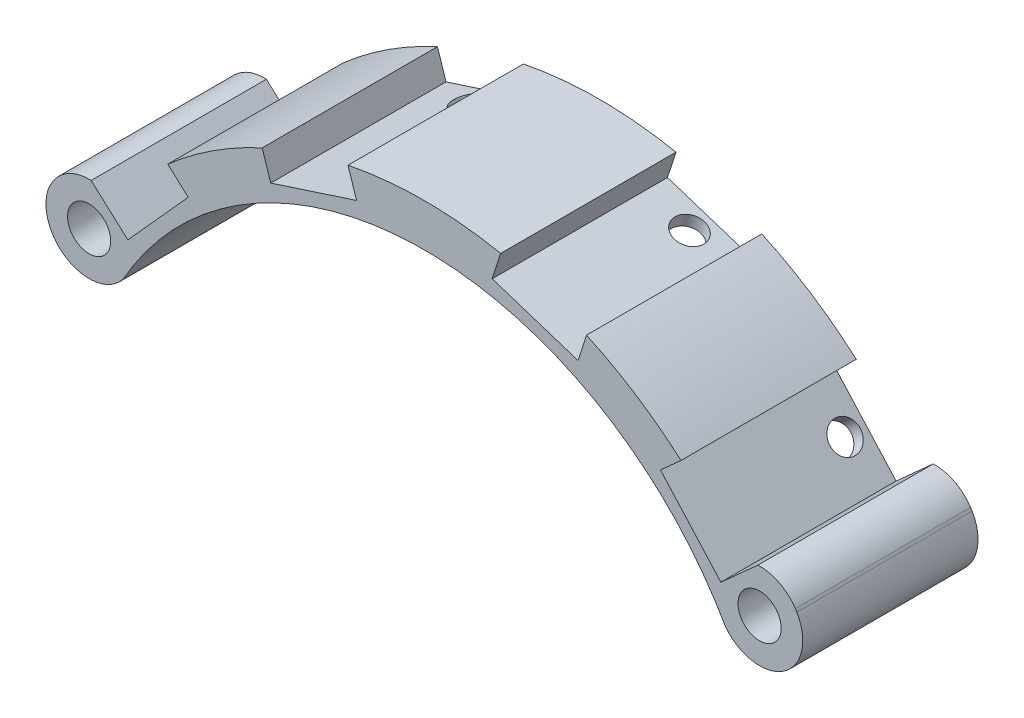
SolidWorks part; units mm, degrees
ref_plane "Plano frontal" through (0, 0, 0) normal (0, 0, 1) x (1, 0, 0)
ref_plane "Plano superior" through (0, 0, 0) normal (0, 1, 0) x (1, 0, 0)
ref_plane "Plano direito" through (0, 0, 0) normal (1, 0, 0) x (0, 0, -1)
sketch "Esboço1" plane through (0, 0, 0) normal (0, 0, 1) x (1, 0, 0)
  line L0 (0, 0) -> (0, 51.8382) construction
  line L1 (-61.8649, 0) -> (70.1374, 0) construction
  line L2 (0, 0) -> (48.4294, 43.606) construction
  line L3 (0, 0) -> (18.6666, 57.4499) construction
  line L4 (-55.5468, 22.7526) -> (83.0962, 22.7526) construction
  line L5 (-20.3288, 62.5655) -> (0, 0) construction
  line L6 (0, 0) -> (-54.7023, 49.2541) construction
  line L7 (-41.8443, -34.4093) -> (54.6077, -34.4093) construction
  circle A0 centre (0, 0) radius 50
  circle A1 centre (-38.8242, 22.7526) radius 2.5
  circle A2 centre (38.8242, 22.7526) radius 2.5
  circle A3 centre (-29, -34.4093) radius 2.5
  circle A5 centre (29, -34.4093) radius 2.5
  dimension "D1" = 42
  dimension "D5" = 58
  dimension "D2" = 30
  dimension "D3" = 18
  dimension "D4" = 30
  dimension "D6" = 45
  dimension "D7" = 45
  dimension "D8" = 58
  dimension "D9" = 58
  dimension "D10" = 45
  dimension "D11" = 45
sketch "Esboço2" plane through (0, 0, 0) normal (0, 0, 1) x (1, 0, 0)
  arc A0 (43.138, 25.2807) -> (-43.138, 25.2807) centre (0, 0) ccw
  circle A2 centre (-38.8242, 22.7526) radius 2.5
  arc A4 (-43.138, 25.2807) -> (-34.8852, 19.6729) centre (-38.8242, 22.7526) ccw
  circle A5 centre (38.8242, 22.7526) radius 2.5
  arc A6 (34.8852, 19.6729) -> (43.138, 25.2807) centre (38.8242, 22.7526) ccw
  circle A8 centre (0, 0) radius 41.6 construction
  arc A9 (34.8852, 19.6729) -> (-34.8852, 19.6729) centre (0, 0) ccw
extrude "Ressalto-extrusão1" add sketch "Esboço2" along normal blind 20.3
ref_plane "Plano1" through (15.4508, 47.5528, 0) normal (0.309, 0.9511, 0) x (0.9511, -0.309, 0)
ref_plane "Plano2" through (37.1572, 33.4565, 0) normal (0.7431, 0.6691, 0) x (0, 0, -1)
ref_plane "Plano3" through (-15.4508, 47.5528, 0) normal (-0.309, 0.9511, 0) x (0.9511, 0.309, 0)
ref_plane "Plano4" through (-37.1572, 33.4565, 0) normal (-0.7431, 0.6691, 0) x (0, 0, 1)
sketch "Esboço3" plane through (15.4508, 47.5528, 0) normal (0.309, 0.9511, 0) x (0.9511, -0.309, 0)
  line L0 (-29.1632, 0) -> (62.5681, 0) construction
  line L1 (-4.9893, 0) -> (4.4995, 0)
  line L2 (-4.9893, 0) -> (-4.9893, -20.3)
  line L3 (-4.9893, -20.3) -> (4.4995, -20.3)
  line L4 (4.4995, 0) -> (4.4995, -20.3)
  line L5 (-48.8388, -20.3) -> (33.2145, -20.3) construction
  circle A0 centre (0, -2.42) radius 1.75
  dimension "D1" = 17.88
  dimension "D2" = 3.5
extrude "Corte-extrusão1" cut sketch "Esboço3" against normal blind 20.3 contours A0
sketch "Esboço4" plane through (15.4508, 47.5528, 0) normal (0.309, 0.9511, 0) x (0.9511, -0.309, 0)
  line L0 (-29.1632, 0) -> (62.5681, 0) construction
  line L1 (-5.225, 0) -> (5.225, 0)
  line L2 (-5.225, 0) -> (-5.225, -20.3)
  line L3 (-5.225, -20.3) -> (5.225, -20.3)
  line L4 (5.225, 0) -> (5.225, -20.3)
  line L12 (-48.8388, -20.3) -> (33.2145, -20.3) construction
  dimension "D1" = 10.45
extrude "Corte-extrusão3" cut sketch "Esboço4" against normal blind 8.5
sketch "Esboço5" plane through (37.1572, 33.4565, 0) normal (0.7431, 0.6691, 0) x (0, 0, -1)
  line L0 (-20.3, 20.3381) -> (-20.3, -10.0777) construction
  line L1 (-20.3, 5.225) -> (0, 5.225)
  line L2 (-20.3, 5.225) -> (-20.3, -5.225)
  line L3 (-20.3, -5.225) -> (0, -5.225)
  line L4 (0, 5.225) -> (0, -5.225)
  line L5 (0, 2.4282) -> (0, -62.1108) construction
  dimension "D1" = 10.45
extrude "Corte-extrusão4" cut sketch "Esboço5" against normal blind 8.5
sketch "Esboço6" plane through (-15.4508, 47.5528, 0) normal (-0.309, 0.9511, 0) x (0.9511, 0.309, 0)
  line L0 (-50.4293, 0) -> (41.3019, 0) construction
  line L1 (-5.225, 0) -> (5.225, 0)
  line L2 (-5.225, 0) -> (-5.225, -20.3)
  line L3 (-5.225, -20.3) -> (5.225, -20.3)
  line L4 (5.225, 0) -> (5.225, -20.3)
  line L5 (-33.2145, -20.3) -> (25.0012, -20.3) construction
  dimension "D1" = 10.45
extrude "Corte-extrusão5" cut sketch "Esboço6" against normal blind 8.5
sketch "Esboço7" plane through (-37.1572, 33.4565, 0) normal (-0.7431, 0.6691, 0) x (0, 0, 1)
  line L0 (0, -53.5704) -> (0, 10.9686) construction
  line L1 (0, 5.225) -> (20.3, 5.225)
  line L2 (0, 5.225) -> (0, -5.225)
  line L3 (0, -5.225) -> (20.3, -5.225)
  line L4 (20.3, 5.225) -> (20.3, -5.225)
  line L5 (20.3, -10.0777) -> (20.3, 20.3381) construction
  dimension "D1" = 10.45
extrude "Corte-extrusão6" cut sketch "Esboço7" against normal blind 8.5
sketch "Esboço8" plane through (30.8405, 27.7689, 0) normal (0.7431, 0.6691, 0) x (0, 0, -1)
  line L0 (-20.3, 5.225) -> (-20.3, -5.225) construction
  circle A0 centre (-2.42, 0) radius 1.75
  dimension "D1" = 17.88
extrude "Corte-extrusão7" cut sketch "Esboço8" against normal blind 8
sketch "Esboço9" plane through (-12.8242, 39.4688, 0) normal (-0.309, 0.9511, 0) x (0.9511, 0.309, 0)
  line L0 (-5.225, -20.3) -> (5.225, -20.3) construction
  circle A0 centre (0, -2.42) radius 1.75
  dimension "D1" = 17.88
sketch "Esboço10" plane through (-30.8405, 27.7689, 0) normal (-0.7431, 0.6691, 0) x (0, 0, 1)
  line L0 (20.3, -5.225) -> (20.3, 5.225) construction
  circle A0 centre (2.42, 0) radius 1.75
  dimension "D1" = 17.88
extrude "Corte-extrusão8" cut sketch "Esboço10" against normal blind 8
extrude "Corte-extrusão9" cut sketch "Esboço9" against normal blind 8
sketch "Esboço11" plane through (0, 0, 20.3) normal (0, 0, 1) x (1, 0, 0)
  line L3 (-40.45, 29.3904) -> (-38.5933, 27.7187)
  line L4 (-34.3367, 23.886) -> (-40.45, 29.3904) construction
  line L5 (-40.45, 29.3904) -> (-42.3273, 29.3904)
  line L6 (-42.3273, 29.3904) -> (-43.3775, 24.7483)
  line L7 (38.6295, 27.7512) -> (40.45, 29.3904)
  line L8 (34.3367, 23.886) -> (40.45, 29.3904) construction
  line L9 (40.45, 29.3904) -> (42.7956, 28.9742)
  line L10 (42.7956, 28.9742) -> (42.9699, 25.5521)
  arc A1 (42.9699, 25.5521) -> (38.6295, 27.7512) centre (38.8242, 22.7526) ccw
  arc A4 (-38.5933, 27.7187) -> (-43.3775, 24.7483) centre (-38.8242, 22.7526) ccw
extrude "Corte-extrusão10" cut sketch "Esboço11" against normal through all
sketch "Esboço13" plane through (0, 0, 20.3) normal (0, 0, 1) x (1, 0, 0)
  line L0 (-43.591, 44.3872) -> (-0.0848, 65.0506)
  line L1 (-0.0848, 65.0506) -> (44.4707, 40.9163)
  line L2 (44.4707, 40.9163) -> (33.1157, 30.4689)
  line L3 (-43.591, 44.3872) -> (-33.7315, 29.7857)
  arc A0 (33.1157, 30.4689) -> (-33.7315, 29.7857) centre (0, 0) ccw
  dimension "D1" = 45
extrude "Corte-extrusão13" cut sketch "Esboço13" against normal through all
